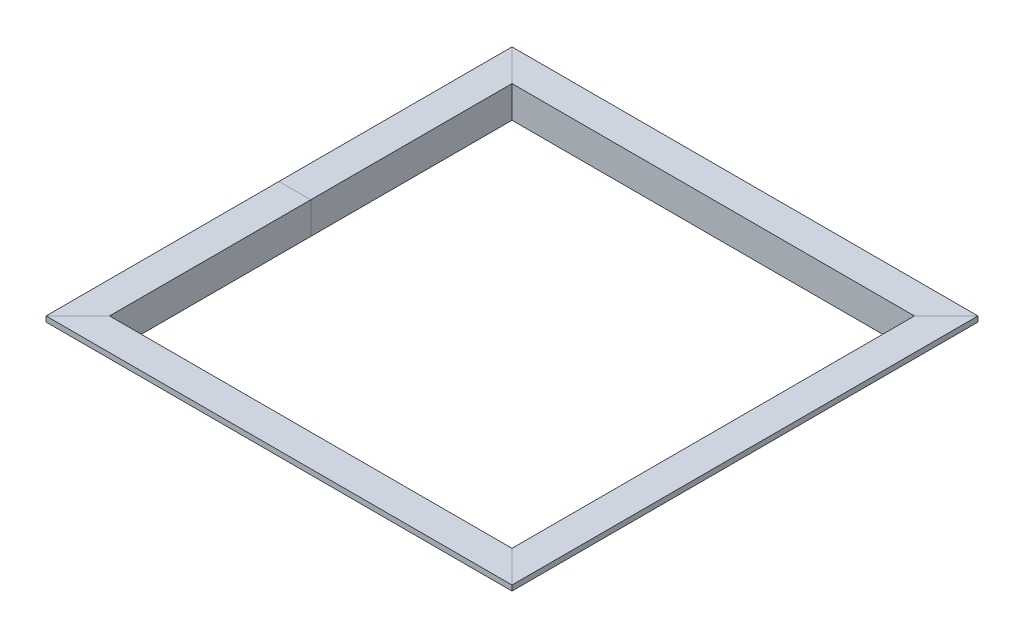
SolidWorks part; units mm, degrees
ref_plane "Front Plane" through (0, 0, 0) normal (0, 0, 1) x (1, 0, 0)
ref_plane "Top Plane" through (0, 0, 0) normal (0, 1, 0) x (1, 0, 0)
ref_plane "Right Plane" through (0, 0, 0) normal (1, 0, 0) x (0, 0, -1)
sketch "Sketch1" plane through (0, 0, 0) normal (0, 1, 0) x (1, 0, 0)
  line L1 (279.4, -279.4) -> (-279.4, -279.4)
  line L2 (279.4, -279.4) -> (279.4, 279.4)
  line L3 (279.4, 279.4) -> (-279.4, 279.4)
  line L4 (-279.4, -279.4) -> (-279.4, 279.4)
  line L5 (279.4, -279.4) -> (-279.4, 279.4) construction
  line L6 (279.4, 279.4) -> (-279.4, -279.4) construction
  point P0 (0, 0)
  dimension "D1" = 558.8
sketch "Sketch2" plane through (0, 0, 0) normal (0, 0, 1) x (1, 0, 0)
  line L0 (-279.4, 0) -> (-241.3, 0)
  line L1 (279.4, 0) -> (-279.4, 0) construction
  line L2 (279.4, 0) -> (-279.4, 0) construction
  line L3 (279.4, 0) -> (-279.4, 0) construction
  line L4 (-241.3, 0) -> (-241.3, -38.1)
  line L5 (-241.3, -38.1) -> (-247.65, -38.1)
  line L6 (-247.65, -38.1) -> (-247.65, -6.35)
  line L7 (-247.65, -6.35) -> (-279.4, -6.35)
  line L8 (-279.4, -6.35) -> (-279.4, 0)
  point P8 (-222.9258, 0)
  point P13 (0, 0)
  dimension "D1" = 38.1
  dimension "D2" = 6.35
sweep "Sweep1" add profiles "Sketch2" path "Sketch1"
